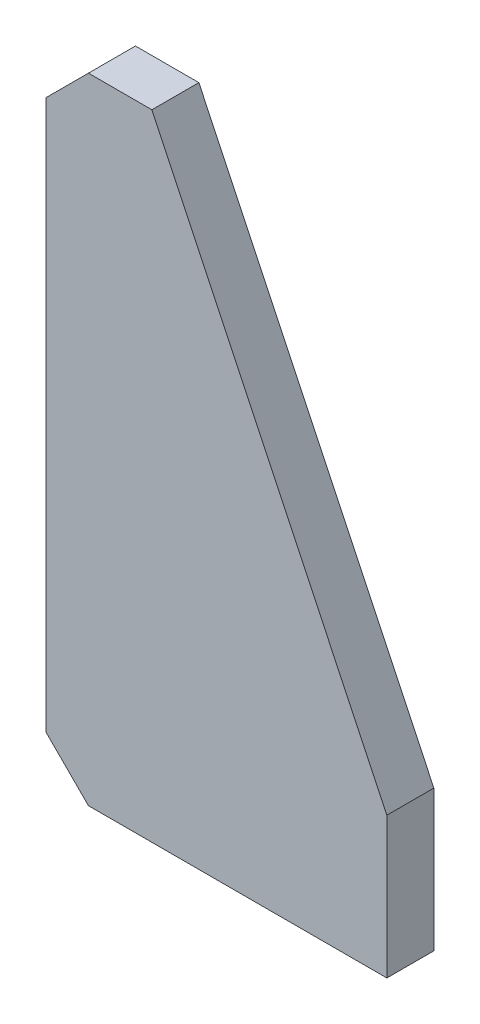
SolidWorks part; units mm, degrees
ref_plane "Спереди" through (0, 0, 0) normal (0, 0, 1) x (1, 0, 0)
ref_plane "Сверху" through (0, 0, 0) normal (0, 1, 0) x (1, 0, 0)
ref_plane "Справа" through (0, 0, 0) normal (1, 0, 0) x (0, 0, -1)
sketch "Эскиз1" plane through (0, 0, 0) normal (0, 0, 1) x (1, 0, 0)
  line L0 (0, 0) -> (0, 60)
  line L1 (0, 60) -> (-100, 270)
  line L2 (-100, 270) -> (-127, 270)
  line L3 (-145, 252) -> (-145, 18)
  line L4 (-127, 0) -> (0, 0)
  line L5 (-127, 270) -> (-145, 252)
  line L6 (-127, 0) -> (-145, 18)
extrude "Бобышка-Вытянуть1" add sketch "Эскиз1" along normal blind 20
